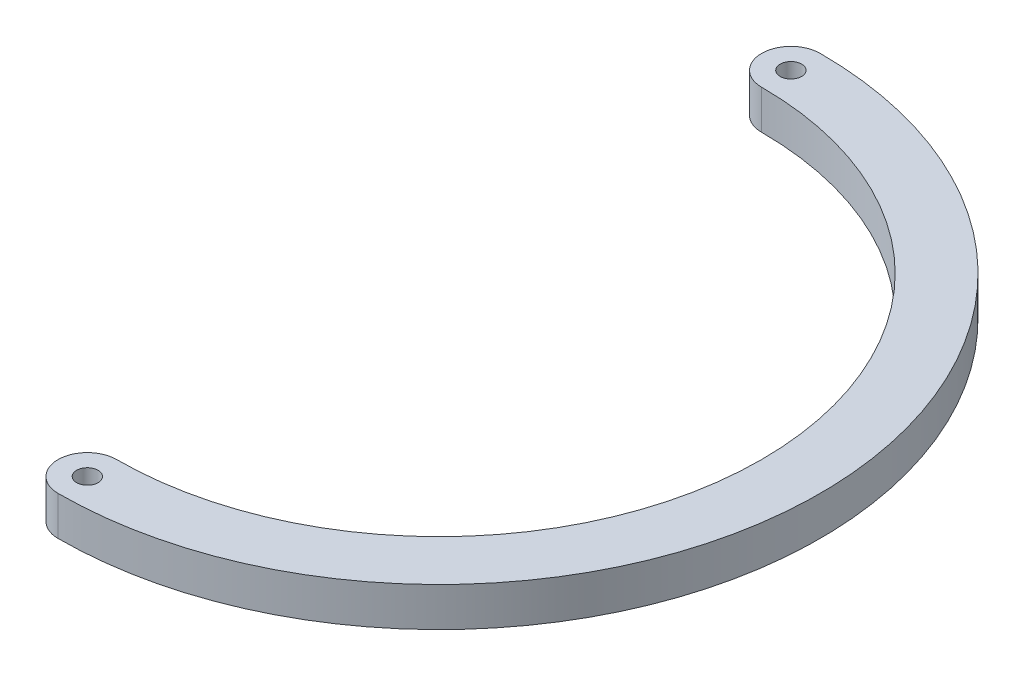
SolidWorks part; units mm, degrees
ref_plane "Front Plane" through (0, 0, 0) normal (0, 0, 1) x (1, 0, 0)
ref_plane "Top Plane" through (0, 0, 0) normal (0, 1, 0) x (1, 0, 0)
ref_plane "Right Plane" through (0, 0, 0) normal (1, 0, 0) x (0, 0, -1)
sketch "Sketch1" plane through (0, 0, 0) normal (0, 1, 0) x (1, 0, 0)
  line L0 (0, 97.55) -> (0, -97.55) construction
  arc A0 (0, -82.55) -> (0, 82.55) centre (0, 0) ccw
  arc A1 (0, -97.55) -> (0, 97.55) centre (0, 0) ccw
  circle A2 centre (0, 0) radius 97.55 construction
  circle A3 centre (0, 0) radius 82.55 construction
  arc A4 (0, 97.55) -> (0, 82.55) centre (0, 90.05) ccw
  arc A5 (0, -82.55) -> (0, -97.55) centre (0, -90.05) ccw
  point P12 (0, 90.05)
  point P13 (0, -90.05)
  dimension "D2" = 165.1
  dimension "D1" = 15
extrude "Boss-Extrude1" add sketch "Sketch1" along normal mid plane 10
hole_wizard "M5 Clearance Hole1" positions "Sketch2" profile "Sketch3" hole size "M5" standard "ANSI Metric" end condition through all
sketch "Sketch2" plane through (0, 5, 0) normal (0, 1, 0) x (1, 0, 0)
  point P0 (0, 90.05)
  point P3 (0, -90.05)
sketch "Sketch3" plane through (0, 5, -90.05) normal (1, 0, 0) x (0, 0, 1)
  line L0 (0, 0) -> (0, 10)
  line L1 (0, 10) -> (2.75, 10)
  line L2 (2.75, 10) -> (2.75, 0)
  line L5 (2.75, 0) -> (0, 0)
  line L11 (0, -6.35) -> (0, 107.95) construction
  dimension "Thru Hole Dia." = 5.5
  dimension "Thru Hole Depth" = 10
equation "\"D2@Sketch1\"=152.40 + (6.35*2)"
